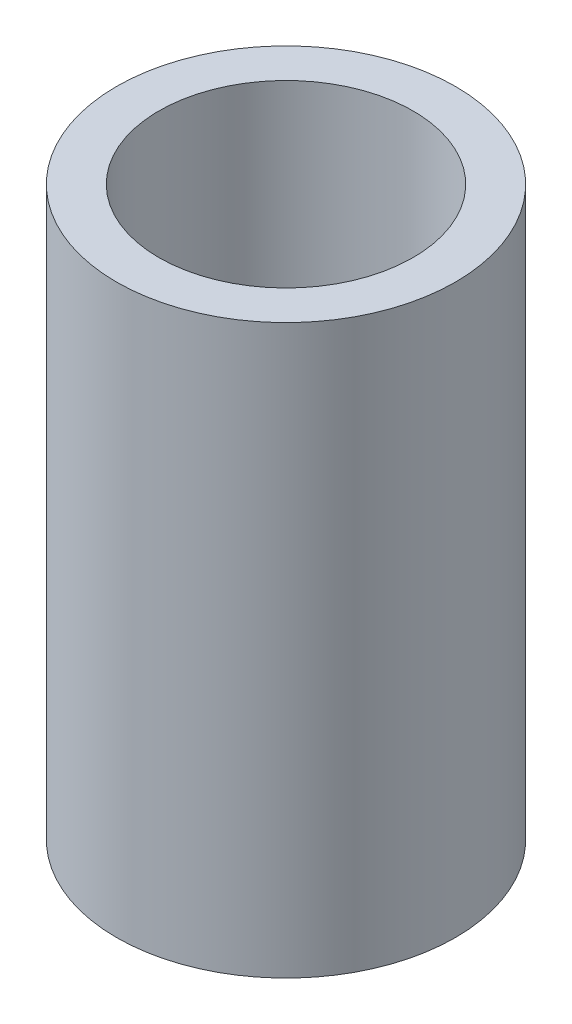
SolidWorks part; units mm, degrees
ref_plane "Front Plane" through (0, 0, 0) normal (0, 0, 1) x (1, 0, 0)
ref_plane "Top Plane" through (0, 0, 0) normal (0, 1, 0) x (1, 0, 0)
ref_plane "Right Plane" through (0, 0, 0) normal (1, 0, 0) x (0, 0, -1)
sketch "Sketch1" plane through (0, 0, 0) normal (0, 1, 0) x (1, 0, 0)
  circle A0 centre (0, 0) radius 1.5
  circle A2 centre (0, 0) radius 2
  dimension "D1" = 3
  dimension "D2" = 4
extrude "Boss-Extrude1" add sketch "Sketch1" along normal blind 6.7
